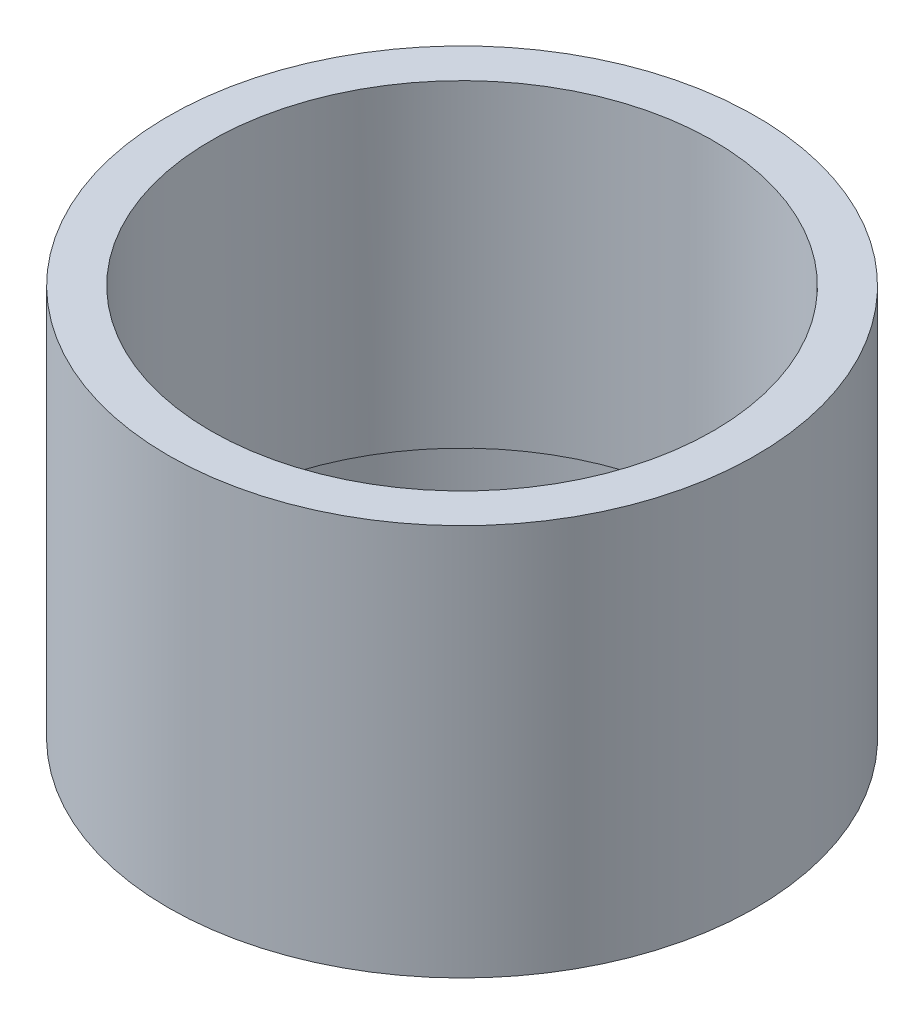
SolidWorks part; units mm, degrees
ref_plane "Front Plane" through (0, 0, 0) normal (0, 0, 1) x (1, 0, 0)
ref_plane "Top Plane" through (0, 0, 0) normal (0, 1, 0) x (1, 0, 0)
ref_plane "Right Plane" through (0, 0, 0) normal (1, 0, 0) x (0, 0, -1)
sketch "Sketch1" plane through (0, 0, 0) normal (0, 1, 0) x (1, 0, 0)
  circle A0 centre (0, 0) radius 33.0835
  circle A1 centre (0, 0) radius 38.1
  dimension "D1" = 66.167
  dimension "D2" = 76.2
extrude "Boss-Extrude1" add sketch "Sketch1" against normal blind 9.525
sketch "Sketch2" plane through (0, 0, 0) normal (0, 1, 0) x (1, 0, 0)
  line L0 (-1.5875, 29.0251) -> (-1.5875, 21.7087)
  line L1 (0, 0) -> (0, 32.5882) construction
  line L2 (1.5875, 29.0251) -> (1.5875, 21.7087)
  line L3 (25.9302, -13.1377) -> (19.5941, -9.4796)
  line L4 (24.3427, -15.8874) -> (18.0066, -12.2292)
  line L5 (-24.3427, -15.8874) -> (-18.0066, -12.2292)
  line L6 (-25.9302, -13.1377) -> (-19.5941, -9.4796)
  circle A0 centre (0, 0) radius 38.1
  arc A1 (-5.2766, 32.1582) -> (-30.4881, -11.5094) centre (0, 0) ccw
  arc A2 (-4.0821, 18.6075) -> (-18.1556, -5.7685) centre (0, 0) ccw
  arc A3 (-5.2766, 32.1582) -> (-1.5875, 29.0251) centre (-4.7625, 29.0251) cw
  arc A4 (-4.0821, 18.6075) -> (-1.5875, 21.7087) centre (-4.7625, 21.7087) ccw
  arc A5 (4.0821, 18.6075) -> (1.5875, 21.7087) centre (4.7625, 21.7087) cw
  arc A6 (5.2766, 32.1582) -> (1.5875, 29.0251) centre (4.7625, 29.0251) ccw
  arc A7 (30.4881, -11.5094) -> (25.9302, -13.1377) centre (27.5177, -10.3881) cw
  arc A8 (18.1556, -5.7685) -> (19.5941, -9.4796) centre (21.1816, -6.7299) ccw
  arc A9 (14.0735, -12.839) -> (18.0066, -12.2292) centre (16.4191, -14.9788) cw
  arc A10 (25.2115, -20.6487) -> (24.3427, -15.8874) centre (22.7552, -18.637) ccw
  arc A11 (-25.2115, -20.6487) -> (-24.3427, -15.8874) centre (-22.7552, -18.637) cw
  arc A12 (-14.0735, -12.839) -> (-18.0066, -12.2292) centre (-16.4191, -14.9788) ccw
  arc A13 (-18.1556, -5.7685) -> (-19.5941, -9.4796) centre (-21.1816, -6.7299) cw
  arc A14 (-30.4881, -11.5094) -> (-25.9302, -13.1377) centre (-27.5177, -10.3881) ccw
  arc A15 (18.1556, -5.7685) -> (4.0821, 18.6075) centre (0, 0) ccw
  arc A16 (-14.0735, -12.839) -> (14.0735, -12.839) centre (0, 0) ccw
  arc A17 (-25.2115, -20.6487) -> (25.2115, -20.6487) centre (0, 0) ccw
  arc A18 (30.4881, -11.5094) -> (5.2766, 32.1582) centre (0, 0) ccw
  circle A19 centre (0, 0) radius 15.875
  point P44 (0, 0)
  dimension "D1" = 65.1764
  dimension "D2" = 76.2
  dimension "D3" = 38.1
  dimension "D5" = 3.175
  dimension "D6" = 3.175
  dimension "D8" = 31.75
  dimension "D4" = 1.5875
  dimension "D7" = 3
extrude "Boss-Extrude2" add sketch "Sketch2" along normal blind 3.175
sketch "Sketch4" plane through (0, 3.175, 0) normal (0, 1, 0) x (1, 0, 0)
  circle A0 centre (0, 0) radius 32.5882
  circle A1 centre (0, 0) radius 38.1
extrude "Boss-Extrude3" add sketch "Sketch4" along normal blind 38.1
